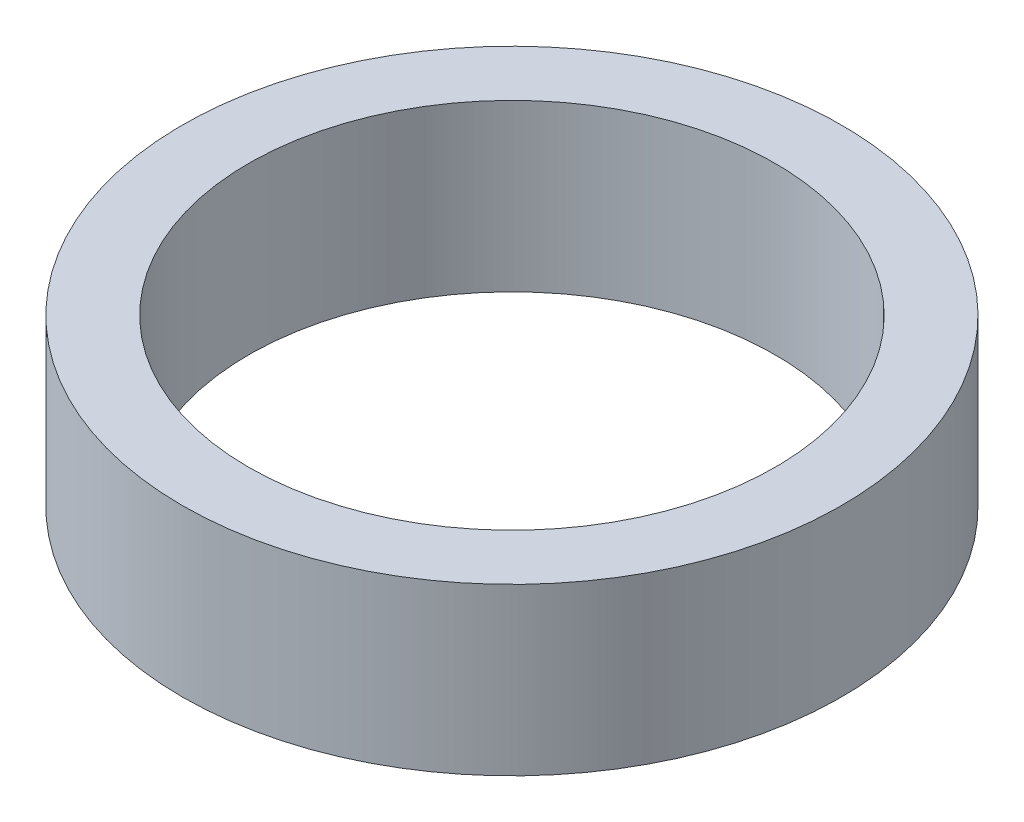
SolidWorks part; units mm, degrees
ref_plane "Front Plane" through (0, 0, 0) normal (0, 0, 1) x (1, 0, 0)
ref_plane "Top Plane" through (0, 0, 0) normal (0, 1, 0) x (1, 0, 0)
ref_plane "Right Plane" through (0, 0, 0) normal (1, 0, 0) x (0, 0, -1)
sketch "Sketch1" plane through (0, 0, 0) normal (0, 1, 0) x (1, 0, 0)
  circle A0 centre (0, 0) radius 15.775
  circle A1 centre (0, 0) radius 12.6
  dimension "D1" = 25.2
  dimension "D2" = 3.175
extrude "Boss-Extrude1" add sketch "Sketch1" along normal mid plane 7.9375
